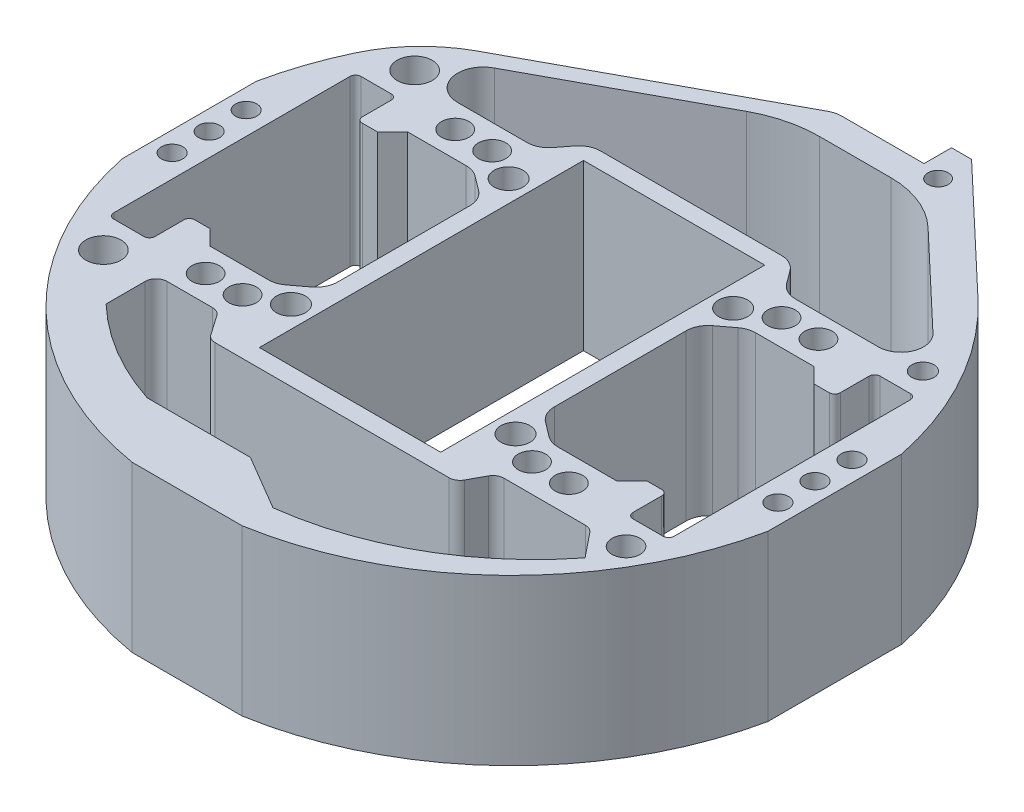
SolidWorks part; units mm, degrees
material "6061 Alloy"
ref_plane "Front Plane" through (0, 0, 0) normal (0, 0, 1) x (1, 0, 0)
ref_plane "Top Plane" through (0, 0, 0) normal (0, 1, 0) x (1, 0, 0)
ref_plane "Right Plane" through (0, 0, 0) normal (1, 0, 0) x (0, 0, -1)
sketch "Sketch1" plane through (0, 0, 0) normal (0, 1, 0) x (1, 0, 0)
  line L0 (-1000, 0) -> (49000, 0) construction
  line L1 (0, -1000) -> (0, 49000) construction
  line L2 (20.955, 37.465) -> (-20.955, 37.465)
  line L3 (-20.955, 37.465) -> (-20.955, 0)
  line L4 (-53.975, 19.3675) -> (-50.4825, 19.3675)
  line L5 (-50.4825, 19.3675) -> (-46.99, 22.86)
  line L6 (-46.99, 22.86) -> (-33.4518, 22.86)
  line L7 (-30.3916, 21.8348) -> (-27.0388, 19.3044)
  line L8 (-74.6125, 15.473) -> (-74.6125, -15.473)
  line L9 (-25.019, 15.2496) -> (-25.019, 0)
  line L10 (74.6125, 15.473) -> (74.6125, -15.473)
  line L11 (0, 76.2) -> (4.1152, 76.2) construction
  line L12 (-55.245, 20.6375) -> (-55.245, 27.305)
  line L13 (-56.515, 28.575) -> (-63.5, 28.575)
  line L14 (-64.77, 27.305) -> (-64.77, -27.305)
  line L15 (64.77, 27.305) -> (64.77, -27.305)
  line L16 (56.515, 28.575) -> (63.5, 28.575)
  line L17 (55.245, 20.6375) -> (55.245, 27.305)
  line L19 (0, 76.2) -> (19.05, 76.2)
  line L20 (25.019, 15.2496) -> (25.019, 0)
  line L21 (-20.846, 41.3381) -> (0, 41.3381)
  line L22 (30.3916, 21.8348) -> (27.0388, 19.3044)
  line L23 (46.99, 22.86) -> (33.4518, 22.86)
  line L24 (46.99, 22.86) -> (50.4825, 19.3675)
  line L25 (53.975, 19.3675) -> (50.4825, 19.3675)
  line L26 (20.955, 37.465) -> (20.955, 0)
  line L27 (20.955, -37.465) -> (20.955, 0)
  line L28 (53.975, -19.3675) -> (50.4825, -19.3675)
  line L29 (46.99, -22.86) -> (50.4825, -19.3675)
  line L30 (46.99, -22.86) -> (33.4518, -22.86)
  line L31 (30.3916, -21.8348) -> (27.0388, -19.3044)
  line L32 (24.9874, 39.2758) -> (27.197, 36.2837)
  line L33 (25.019, -15.2496) -> (25.019, 0)
  line L34 (19.05, 76.2) -> (19.05, 82.55)
  line L35 (19.05, 82.55) -> (23.6855, 82.55)
  line L36 (55.245, -20.6375) -> (55.245, -27.305)
  line L37 (56.515, -28.575) -> (63.5, -28.575)
  line L38 (-56.515, -28.575) -> (-63.5, -28.575)
  line L39 (-55.245, -20.6375) -> (-55.245, -27.305)
  line L40 (-23.8543, -60.4955) -> (0, -60.4955)
  line L41 (52.4298, 55.2951) -> (23.6855, 82.55)
  line L42 (-25.019, -15.2496) -> (-25.019, 0)
  line L43 (31.2835, 34.2214) -> (50.4563, 34.2214)
  line L44 (-30.3916, -21.8348) -> (-27.0388, -19.3044)
  line L45 (-46.99, -22.86) -> (-33.4518, -22.86)
  line L46 (-50.4825, -19.3675) -> (-46.99, -22.86)
  line L47 (-53.975, -19.3675) -> (-50.4825, -19.3675)
  line L48 (-20.955, -37.465) -> (-20.955, 0)
  line L49 (20.955, -37.465) -> (-20.955, -37.465)
  line L50 (-44.8593, -34.8822) -> (-34.3568, -34.8822)
  line L51 (-47.0915, 34.5231) -> (-31.087, 34.5231)
  line L52 (-27.0577, 36.5094) -> (-24.8753, 39.3518)
  line L53 (0, 41.3381) -> (20.9009, 41.3381)
  line L54 (54.0568, 43.2516) -> (32.3487, 63.8349)
  line L55 (18.015, 69.55) -> (1.5516, 69.55)
  line L56 (-32.2697, -35.9746) -> (-29.1259, -40.5071)
  line L57 (-27.0388, -41.5995) -> (27.0388, -41.5995)
  line L58 (-47.3993, -37.4222) -> (-47.3993, -46.4548)
  line L59 (54.276, -36.2937) -> (58.8069, -41.9283)
  line L60 (31.2258, -36.6729) -> (29.2707, -40.272)
  line L61 (52.2966, -35.3453) -> (33.4578, -35.3453)
  line L62 (-11.9532, 66.1301) -> (-49.7073, 45.6984)
  line L63 (-55.1504, 47.0849) -> (-2.539, 75.557)
  line L64 (0, -60.4955) -> (12.7, -67.9689)
  line L65 (12.7, -75.1342) -> (-12.7, -75.1342)
  arc A0 (-55.1504, 47.0849) -> (-68.875, 32.5987) centre (-39.8854, 18.8779) ccw
  arc A1 (63.5, -28.575) -> (64.77, -27.305) centre (63.5, -27.305) ccw
  arc A2 (64.77, 27.305) -> (63.5, 28.575) centre (63.5, 27.305) ccw
  arc A3 (-63.5, -28.575) -> (-64.77, -27.305) centre (-63.5, -27.305) cw
  arc A4 (-63.5, 28.575) -> (-64.77, 27.305) centre (-63.5, 27.305) ccw
  arc A5 (74.6125, 15.473) -> (52.4298, 55.2951) centre (0, 0) ccw
  arc A6 (-74.6125, -15.473) -> (-12.7, -75.1342) centre (0, 0) ccw
  arc A7 (55.245, -27.305) -> (56.515, -28.575) centre (56.515, -27.305) ccw
  arc A8 (56.515, 28.575) -> (55.245, 27.305) centre (56.515, 27.305) ccw
  arc A9 (-56.515, -28.575) -> (-55.245, -27.305) centre (-56.515, -27.305) ccw
  arc A10 (-55.245, 27.305) -> (-56.515, 28.575) centre (-56.515, 27.305) ccw
  arc A15 (50.4563, 34.2214) -> (54.0568, 43.2516) centre (50.4563, 39.4543) ccw
  arc A16 (-49.7073, 45.6984) -> (-47.0915, 34.5231) centre (-47.0915, 40.4169) ccw
  arc A17 (32.3487, 63.8349) -> (18.015, 69.55) centre (18.015, 48.7178) ccw
  arc A18 (-68.875, 32.5987) -> (-74.6125, 15.473) centre (0, 0) ccw
  arc A19 (12.7, -67.9689) -> (58.8069, -41.9283) centre (4.0432, 1.1967) ccw
  arc A20 (-47.3993, -46.4548) -> (-23.8543, -60.4955) centre (-4.9282, -1.9967) ccw
  arc A21 (12.7, -75.1342) -> (74.6125, -15.473) centre (0, 0) ccw
  circle A22 centre (23.6855, 74.8125) radius 2.3565
  circle A23 centre (-25.954, 25.1591) radius 3.3565
  arc A24 (-30.3916, -21.8348) -> (-33.4518, -22.86) centre (-33.4518, -17.78) cw
  arc A25 (-33.4518, 22.86) -> (-30.3916, 21.8348) centre (-33.4518, 17.78) cw
  arc A26 (30.3916, 21.8348) -> (33.4518, 22.86) centre (33.4518, 17.78) cw
  arc A27 (33.4518, -22.86) -> (30.3916, -21.8348) centre (33.4518, -17.78) cw
  arc A28 (27.0388, -19.3044) -> (25.019, -15.2496) centre (30.099, -15.2496) cw
  arc A29 (25.019, 15.2496) -> (27.0388, 19.3044) centre (30.099, 15.2496) cw
  arc A30 (-25.019, -15.2496) -> (-27.0388, -19.3044) centre (-30.099, -15.2496) cw
  arc A31 (-27.0388, 19.3044) -> (-25.019, 15.2496) centre (-30.099, 15.2496) cw
  arc A32 (53.975, -19.3675) -> (55.245, -20.6375) centre (53.975, -20.6375) cw
  arc A34 (55.245, 20.6375) -> (53.975, 19.3675) centre (53.975, 20.6375) cw
  arc A37 (-55.245, -20.6375) -> (-53.975, -19.3675) centre (-53.975, -20.6375) cw
  arc A38 (-53.975, 19.3675) -> (-55.245, 20.6375) centre (-53.975, 20.6375) cw
  circle A40 centre (-41.9877, 28.8501) radius 3.175
  circle A41 centre (41.9877, 28.8501) radius 3.175
  circle A42 centre (-41.9877, -28.8501) radius 3.175
  circle A43 centre (41.9877, -28.8501) radius 3.175
  circle A44 centre (-33.4518, 28.8501) radius 3.175
  circle A45 centre (33.4518, 28.8501) radius 3.175
  circle A46 centre (-33.4518, -28.8501) radius 3.175
  circle A47 centre (33.4518, -28.8501) radius 3.175
  circle A48 centre (-58.4996, 35.9746) radius 4.0647
  circle A49 centre (60.46, 34.5231) radius 2.5554
  circle A50 centre (-58.4996, -35.9746) radius 4.0647
  circle A51 centre (61.2367, -34.8822) radius 3.2423
  circle A52 centre (25.954, 25.1591) radius 3.3565
  circle A53 centre (25.954, -25.1591) radius 3.3565
  circle A54 centre (-25.954, -25.1591) radius 3.3565
  arc A55 (-27.0388, -41.5995) -> (-29.1259, -40.5071) centre (-27.0388, -39.0595) cw
  arc A56 (-34.3568, -34.8822) -> (-32.2697, -35.9746) centre (-34.3568, -37.4222) cw
  circle A57 centre (70.0256, 8.5625) radius 2.4628
  circle A58 centre (-70.0256, 8.5625) radius 2.4628
  circle A59 centre (70.0256, -8.5625) radius 2.4628
  circle A60 centre (-70.0256, -8.5625) radius 2.4628
  arc A61 (54.276, -36.2937) -> (52.2966, -35.3453) centre (52.2966, -37.8853) ccw
  arc A62 (31.2258, -36.6729) -> (33.4578, -35.3453) centre (33.4578, -37.8853) cw
  arc A63 (29.2707, -40.272) -> (27.0388, -41.5995) centre (27.0388, -39.0595) cw
  arc A64 (-44.8593, -34.8822) -> (-47.3993, -37.4222) centre (-44.8593, -37.4222) ccw
  circle A69 centre (-70.0256, 0) radius 2.4628
  circle A70 centre (70.0256, 0) radius 2.4628
  arc A71 (27.197, 36.2837) -> (31.2835, 34.2214) centre (31.2835, 39.3014) ccw
  arc A72 (20.9009, 41.3381) -> (24.9874, 39.2758) centre (20.9009, 36.2581) cw
  arc A73 (-31.087, 34.5231) -> (-27.0577, 36.5094) centre (-31.087, 39.6031) ccw
  arc A74 (-24.8753, 39.3518) -> (-20.846, 41.3381) centre (-20.846, 36.2581) cw
  arc A75 (-11.9532, 66.1301) -> (1.5516, 69.55) centre (1.5516, 41.1755) cw
  arc A76 (-2.539, 75.557) -> (0, 76.2) centre (0, 70.8654) cw
  point P34 (0, 37.465)
  point P44 (64.77, -28.575)
  point P49 (64.77, 0)
  point P50 (-64.77, 0)
  point P52 (55.245, -28.575)
  point P62 (64.77, 28.575)
  point P65 (-64.77, -28.575)
  point P68 (-64.77, 28.575)
  point P70 (-74.6125, 0)
  point P96 (-31.75, -22.86)
  point P99 (55.245, 28.575)
  point P103 (-55.245, -28.575)
  point P106 (-55.245, 28.575)
  point P111 (-48.26, -22.86)
  point P114 (48.26, -22.86)
  point P117 (48.26, 22.86)
  point P120 (-48.26, 22.86)
  point P124 (-31.75, 22.86)
  point P127 (31.75, 22.86)
  point P130 (31.75, -22.86)
  point P133 (25.019, -17.78)
  point P136 (25.019, 17.78)
  point P139 (-25.019, -17.78)
  point P142 (-25.019, 17.78)
  point P145 (55.245, -19.3675)
  point P148 (48.26, -19.3675)
  point P151 (55.245, 19.3675)
  point P154 (48.26, 19.3675)
  point P157 (-48.26, -19.3675)
  point P160 (-55.245, -19.3675)
  point P163 (-55.245, 19.3675)
  point P166 (-48.26, 19.3675)
  point P195 (0, -41.5995)
  point P218 (53.5134, -35.3453)
  point P221 (31.947, -35.3453)
  point P224 (28.5496, -41.5995)
  point P258 (-5.6338, 69.55)
  dimension "D2" = 41.91
  dimension "D7" = 1.27
  dimension "D10" = 1.27
  dimension "D16" = 21.971
  dimension "D3" = 5.08
  dimension "D22" = 1.27
  dimension "D23" = 2.54
  dimension "D14" = 6.35
  dimension "D24" = 38.735
  dimension "D25" = 5.08
  dimension "D26" = 4.6355
  dimension "D27" = 21.971
  dimension "D19" = 2.54
  dimension "D33" = 45
  dimension "D4" = 16.51
  dimension "D5" = 45.72
  dimension "D6" = 74.93
  dimension "D8" = 149.225
  dimension "D9" = 9.525
  dimension "D11" = 45
  dimension "D12" = 4.064
  dimension "D13" = 57.15
  dimension "D15" = 35.56
  dimension "D18" = 19.05
  dimension "D20" = 7.62
  dimension "D21" = 25.4
  dimension "D28" = 76.2
  dimension "D29" = 3.81
  dimension "D31" = 45
  dimension "D32" = 21.971
  dimension "D34" = 21.971
  dimension "D35" = 45
extrude "Boss-Extrude1" add sketch "Sketch1" along normal blind 38.1
ref_plane "Plane1" through (0, 19.05, 0) normal (0, 1, 0) x (-1, 0, 0)
ref_plane "Plane2" through (0, 0, 0) normal (-1, 0, 0) x (0, 0, 1)
